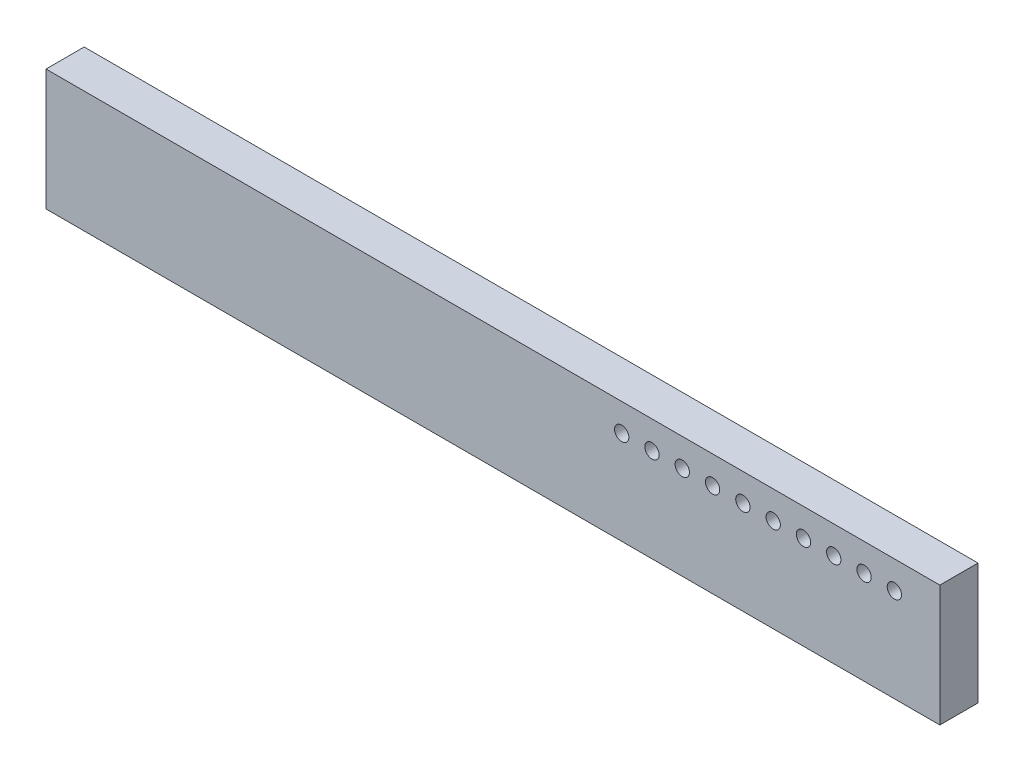
SolidWorks part; units mm, degrees
ref_plane "Front Plane" through (0, 0, 0) normal (0, 0, 1) x (1, 0, 0)
ref_plane "Top Plane" through (0, 0, 0) normal (0, 1, 0) x (1, 0, 0)
ref_plane "Right Plane" through (0, 0, 0) normal (1, 0, 0) x (0, 0, -1)
sketch "Sketch1" plane through (0, 0, 0) normal (0, 0, 1) x (1, 0, 0)
  line L1 (-18.7325, -2.54) -> (18.7325, -2.54)
  line L2 (-18.7325, -2.54) -> (-18.7325, 2.54)
  line L3 (-18.7325, 2.54) -> (18.7325, 2.54)
  line L4 (18.7325, -2.54) -> (18.7325, 2.54)
  line L5 (-18.7325, -2.54) -> (18.7325, 2.54) construction
  line L6 (-18.7325, 2.54) -> (18.7325, -2.54) construction
  point P0 (0, 0)
  dimension "D1" = 37.465
  dimension "D2" = 5.08
extrude "Boss-Extrude1" add sketch "Sketch1" along normal blind 1.6 contours L2 L1 L4 L3
sketch "Sketch2" plane through (0, 0, 1.6) normal (0, 0, 1) x (1, 0, 0)
  line L0 (16.7525, 1.455) -> (16.9025, 1.305) construction
  line L1 (-18.7325, 2.54) -> (-18.7325, -2.54) construction
  line L2 (18.7325, 2.54) -> (-18.7325, 2.54) construction
  line L4 (16.9025, 1.455) -> (16.7525, 1.455)
  line L5 (16.7525, 1.455) -> (16.7525, 1.305)
  line L6 (16.7525, 1.305) -> (16.9025, 1.305)
  line L7 (16.9025, 1.305) -> (16.9025, 1.455)
  line L8 (16.9025, 1.455) -> (16.7525, 1.455)
  line L9 (16.7525, 1.455) -> (16.7525, 1.305)
  line L10 (16.7525, 1.305) -> (16.9025, 1.305)
  line L11 (16.9025, 1.305) -> (16.9025, 1.455)
  circle A0 centre (16.8275, 1.38) radius 0.3
  circle A1 centre (15.5575, 1.38) radius 0.3
  circle A2 centre (14.2875, 1.38) radius 0.3
  circle A3 centre (13.0175, 1.38) radius 0.3
  circle A4 centre (11.7475, 1.38) radius 0.3
  circle A5 centre (10.4775, 1.38) radius 0.3
  circle A6 centre (9.2075, 1.38) radius 0.3
  circle A7 centre (7.9375, 1.38) radius 0.3
  circle A8 centre (6.6675, 1.38) radius 0.3
  circle A9 centre (5.3975, 1.38) radius 0.3
  dimension "D2" = 10
  dimension "D3" = 35.56
  dimension "D4" = 1.16
  dimension "D1" = 0
extrude "Cut-Extrude1" cut sketch "Sketch2" against normal through all
sketch "Sketch3" plane through (0, 0, 1.6) normal (0, 0, 1) x (1, 0, 0)
  line L0 (-18.7325, 2.54) -> (-16.1925, 0) construction
  line L1 (-16.1925, 0) -> (-18.7325, -2.54) construction
  line L2 (0, -0.88) -> (0, 0.88) construction
  line L3 (16.1925, 0) -> (18.7325, -2.54) construction
  line L4 (18.7325, 2.54) -> (16.1925, 0) construction
  line L5 (-16.1925, 0) -> (16.1925, 0) construction
  line L6 (-18.7325, -2.54) -> (-18.7325, 2.54) construction
  circle A0 centre (16.8275, 1.38) radius 0.3 construction
  point P10 (-15.3925, 0)
  point P11 (-9.2355, 0)
  point P14 (-3.0785, 0)
  point P15 (3.0785, 0)
  point P16 (9.2355, 0)
  point P17 (15.3925, 0)
  dimension "D11" = 35.56
  dimension "D1" = 0.8
  dimension "D3" = 0.8
  dimension "D4" = 3.34
  dimension "D5" = 9.497
  dimension "D6" = 15.654
  dimension "D7" = 21.811
  dimension "D8" = 27.968
  dimension "D9" = 34.125
  dimension "D10" = 6.157
  dimension "D12" = 1.16
  dimension "D2" = 6
